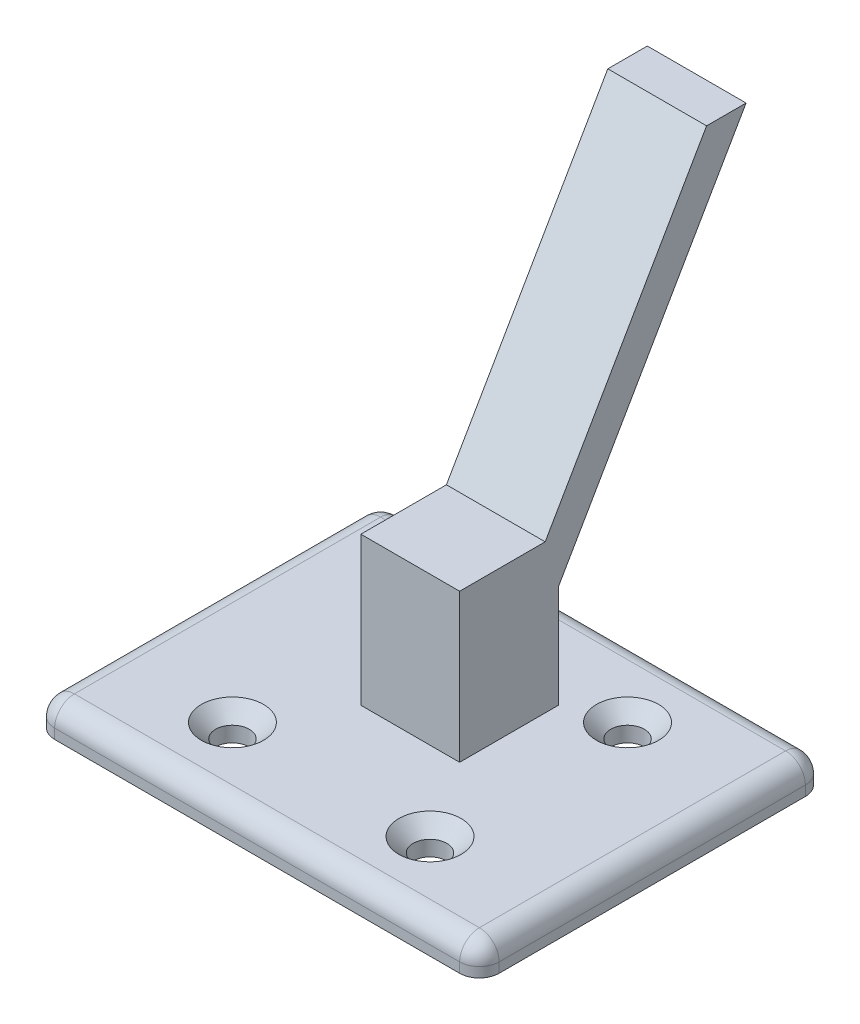
SolidWorks part; units mm, degrees
ref_plane "Front Plane" through (0, 0, 0) normal (0, 0, 1) x (1, 0, 0)
ref_plane "Top Plane" through (0, 0, 0) normal (0, 1, 0) x (1, 0, 0)
ref_plane "Right Plane" through (0, 0, 0) normal (1, 0, 0) x (0, 0, -1)
sketch "Sketch1" plane through (0, 0, 0) normal (0, 1, 0) x (1, 0, 0)
  line L1 (22.5, 17.5) -> (-22.5, 17.5)
  line L2 (22.5, 17.5) -> (22.5, -17.5)
  line L3 (22.5, -17.5) -> (-22.5, -17.5)
  line L4 (-22.5, 17.5) -> (-22.5, -17.5)
  line L5 (22.5, 17.5) -> (-22.5, -17.5) construction
  line L6 (22.5, -17.5) -> (-22.5, 17.5) construction
  point P0 (0, 0)
  dimension "D1" = 35
  dimension "D2" = 45
extrude "Boss-Extrude1" add sketch "Sketch1" along normal blind 3
sketch "Sketch2" plane through (0, 3, 0) normal (0, 1, 0) x (1, 0, 0)
  line L0 (-22.5, -17.5) -> (22.5, -17.5) construction
  line L1 (-22.5, 17.5) -> (-22.5, -17.5) construction
  line L2 (0, 17.5) -> (0, -17.5) construction
  line L3 (22.5, 17.5) -> (-22.5, 17.5) construction
  line L4 (-22.5, 0) -> (22.5, 0) construction
  line L5 (22.5, -17.5) -> (22.5, 17.5) construction
  point P0 (-10, -10)
  point P13 (10, -10)
  point P14 (10, 10)
  point P15 (-10, 10)
  dimension "D1" = 7.5
  dimension "D2" = 12.5
hole_wizard "CSK for M3 Flat Head Machine Screw2" positions "Sketch6" profile "Sketch5" countersink size "M3" standard "ANSI Metric" end condition up to next
sketch "Sketch6" plane through (0, 3, 0) normal (0, 1, 0) x (1, 0, 0)
  point P0 (10, 10)
  point P3 (-10, 10)
  point P6 (-10, -10)
  point P9 (10, -10)
sketch "Sketch5" plane through (10, 3, -10) normal (1, 0, 0) x (0, 0, 1)
  line L0 (0, 0) -> (0, 3)
  line L1 (0, 3) -> (1.7, 3)
  line L2 (1.7, 3) -> (1.7, 1.45)
  line L3 (1.7, 1.45) -> (3.15, 0)
  line L5 (3.15, 0) -> (0, 0)
  line L6 (-1.7, 1.45) -> (-3.15, 0) construction
  line L11 (0, -6.35) -> (0, 107.95) construction
  dimension "Thru Hole Dia." = 3.4
  dimension "Thru Hole Depth" = 3
  dimension "Near C'Sink Dia." = 6.3
  dimension "Near C'Sink Angle" = 90
sketch "Sketch11" plane through (22.5, 0, 0) normal (1, 0, 0) x (0, 0, -1)
  line L0 (0, 3) -> (17.3912, 33.1225) construction
  line L1 (17.5, 3) -> (-17.5, 3) construction
  dimension "D1" = 60
sketch "Sketch7" plane through (0, 3, 0) normal (0, 1, 0) x (1, 0, 0)
  line L1 (-5, -2) -> (5, -2)
  line L2 (-5, -2) -> (-5, 2)
  line L3 (-5, 2) -> (5, 2)
  line L4 (5, -2) -> (5, 2)
  line L5 (-5, -2) -> (5, 2) construction
  line L6 (-5, 2) -> (5, -2) construction
  point P0 (0, 0)
  dimension "D1" = 4
  dimension "D2" = 10
extrude "Boss-Extrude2" add sketch "Sketch7" along direction (0, 0.866, -0.5) on the side of the normal blind 50 from offset 0
fillet "Fillet1" radius 2 8 edges at (-22.5, 3, 0) (0, 3, -17.5) (22.5, 3, 0) (0, 3, 17.5) (-22.5, 1.5, -17.5) (22.5, 1.5, -17.5) (-22.5, 1.5, 17.5) (22.5, 1.5, 17.5)
sketch "Sketch12" plane through (0, 3, 0) normal (0, 1, 0) x (1, 0, 0)
  line L0 (5, 23) -> (5, -2) construction
  line L1 (-5, -2) -> (5, -2)
  line L2 (-5, -2) -> (-5, 8)
  line L3 (-5, 8) -> (5, 8)
  line L4 (5, -2) -> (5, 8)
  dimension "D1" = 10
extrude "Boss-Extrude3" add sketch "Sketch12" along normal blind 15
